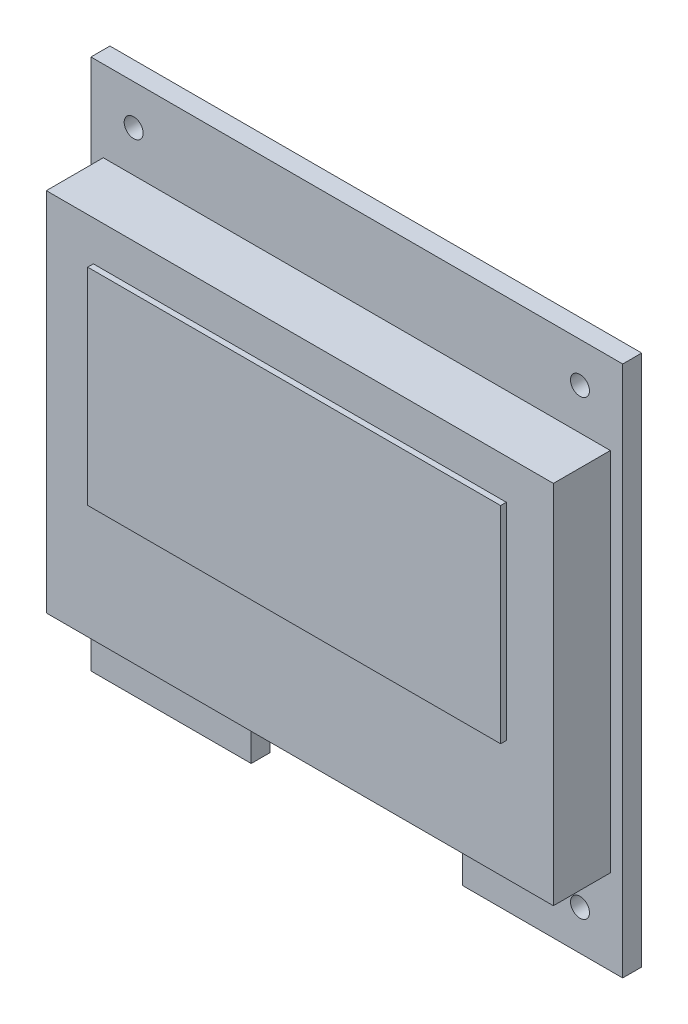
SolidWorks part; units mm, degrees
ref_plane "Plan de face" through (0, 0, 0) normal (0, 0, 1) x (1, 0, 0)
ref_plane "Plan de dessus" through (0, 0, 0) normal (0, 1, 0) x (1, 0, 0)
ref_plane "Plan de droite" through (0, 0, 0) normal (1, 0, 0) x (0, 0, -1)
sketch "Esquisse1" plane through (0, 0, 0) normal (0, 0, 1) x (1, 0, 0)
  line L0 (3.0655, 15.6539) -> (3.0655, -12.3985) construction
  line L1 (-10.9345, 15.6539) -> (17.0655, 15.6539)
  line L2 (-10.9345, 15.6539) -> (-10.9345, -12.3461)
  line L3 (-10.9345, -12.3461) -> (-2.495, -12.3461)
  line L4 (17.0655, 15.6539) -> (17.0655, -12.3461)
  line L6 (-2.495, -12.3461) -> (-2.495, -10.3461)
  line L7 (-2.495, -10.3461) -> (3.0655, -10.3461)
  line L8 (8.6259, -12.3461) -> (8.6259, -10.3461)
  line L9 (8.6259, -10.3461) -> (3.0655, -10.3461)
  line L10 (-8.6845, 13.5539) -> (3.0655, 13.5539) construction
  line L11 (14.8155, 13.5539) -> (3.0655, 13.5539) construction
  line L12 (-10.9345, 1.6539) -> (17.0655, 1.6539) construction
  line L13 (-8.6845, 13.5539) -> (-8.6845, 1.6539) construction
  line L14 (-8.6845, 1.6539) -> (-8.6845, -10.2461) construction
  line L15 (8.6259, -12.3461) -> (17.0655, -12.3461)
  circle A0 centre (-8.6845, -10.2461) radius 0.5
  circle A1 centre (-8.6845, 13.5539) radius 0.5
  circle A2 centre (14.8155, 13.5539) radius 0.5
  circle A3 centre (14.8155, -10.2461) radius 0.5
  dimension "D6" = 1
  dimension "D1" = 28
  dimension "D2" = 28
  dimension "D3" = 2
  dimension "D4" = 23.8
  dimension "D5" = 23.5
extrude "Boss.-Extru.1" add sketch "Esquisse1" along normal blind 1
sketch "Esquisse2" plane through (0, 0, 1) normal (0, 0, 1) x (1, 0, 0)
  line L0 (17.0655, 15.6539) -> (-10.9345, 15.6539) construction
  line L1 (-10.2845, 11.3839) -> (16.4155, 11.3839)
  line L2 (-10.2845, 11.3839) -> (-10.2845, -7.8761)
  line L3 (-10.2845, -7.8761) -> (16.4155, -7.8761)
  line L4 (16.4155, 11.3839) -> (16.4155, -7.8761)
  point P4 (3.0655, 11.3839)
  point P7 (3.0655, 15.6539)
  dimension "D1" = 26.7
  dimension "D2" = 19.26
  dimension "D3" = 4.27
extrude "Boss.-Extru.2" add sketch "Esquisse2" along normal blind 3
sketch "Esquisse4" plane through (0, 0, 4) normal (0, 0, 1) x (1, 0, 0)
  line L0 (3.0655, 11.3839) -> (3.0655, -7.8761) construction
  line L1 (-7.8065, 9.2839) -> (13.9375, 9.2839)
  line L2 (-7.8065, 9.2839) -> (-7.8065, -1.5801)
  line L3 (-7.8065, -1.5801) -> (13.9375, -1.5801)
  line L4 (13.9375, 9.2839) -> (13.9375, -1.5801)
  line L5 (16.4155, 11.3839) -> (-10.2845, 11.3839) construction
  line L6 (-10.2845, -7.8761) -> (16.4155, -7.8761) construction
  point P10 (3.0655, 9.2839)
  dimension "D1" = 21.744
  dimension "D2" = 10.864
  dimension "D3" = 2.1
extrude "Boss.-Extru.3" add sketch "Esquisse4" along normal blind 0.3
sketch "Esquisse5" plane through (0, 0, 4.3) normal (0, 0, 1) x (1, 0, 0)
  line L0 (3.0655, 9.2839) -> (3.0655, -1.5801) construction
  line L1 (13.9375, 9.2839) -> (-7.8065, 9.2839) construction
  line L2 (-7.8065, -1.5801) -> (13.9375, -1.5801) construction
  line L3 (-7.8065, 3.8519) -> (13.9375, 3.8519) construction
  line L4 (-7.8065, 9.2839) -> (-7.8065, -1.5801) construction
  line L5 (13.9375, -1.5801) -> (13.9375, 9.2839) construction
  point P12 (3.0655, 3.8519)
